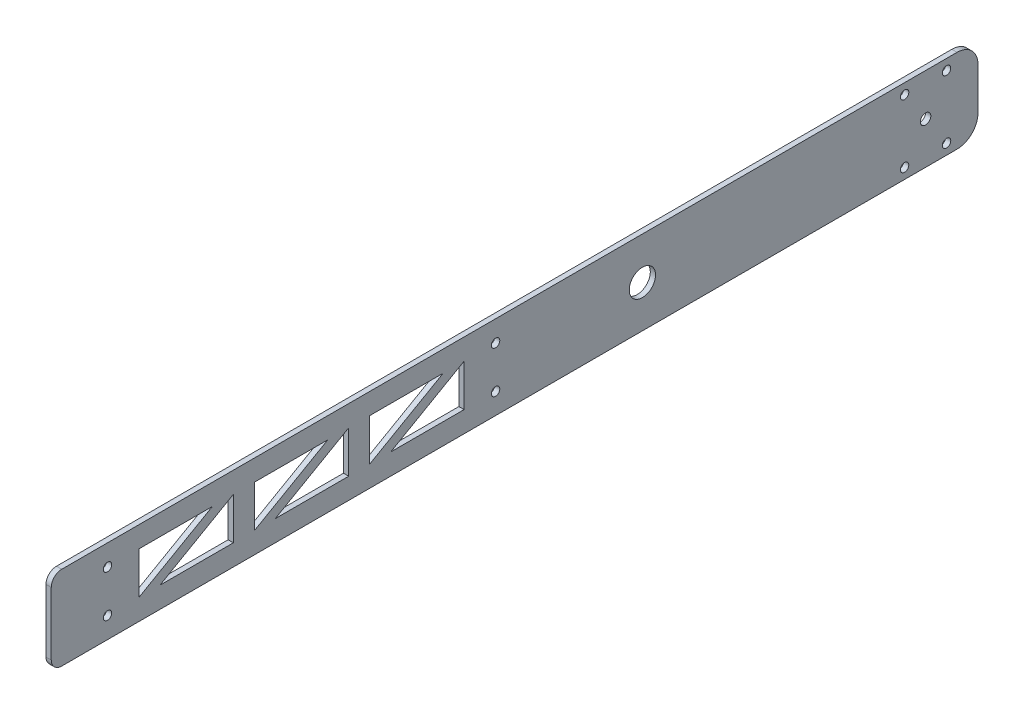
SolidWorks part; units mm, degrees
material "1060 Alloy"
ref_plane "Front Plane" through (0, 0, 0) normal (0, 0, 1) x (1, 0, 0)
ref_plane "Top Plane" through (0, 0, 0) normal (0, 1, 0) x (1, 0, 0)
ref_plane "Right Plane" through (0, 0, 0) normal (1, 0, 0) x (0, 0, -1)
sketch "Sketch1" plane through (0, 0, 0) normal (1, 0, 0) x (0, 0, -1)
  line L0 (177.8, 38.1) -> (177.8, 12.7)
  line L1 (165.1, 0) -> (-571.5, 0)
  line L2 (0, 0) -> (0, 50.8) construction
  line L3 (165.1, 50.8) -> (-571.5, 50.8)
  line L4 (-507.6587, 38.1) -> (372.0993, 38.1) construction
  line L5 (-584.2, 38.1) -> (-584.2, 12.7)
  line L6 (-663.1888, 12.7) -> (-221.2336, 12.7) construction
  line L7 (-190.5, 38.1) -> (-146.05, 38.1)
  line L8 (133.35, 44.45) -> (133.35, 6.35) construction
  line L9 (133.35, 6.35) -> (158.75, 6.35) construction
  line L10 (158.75, 6.35) -> (158.75, 44.45) construction
  line L11 (158.75, 44.45) -> (133.35, 44.45) construction
  line L25 (-349.25, 119.599) -> (-349.25, -64.072) construction
  line L26 (-133.35, 38.1) -> (-133.35, 12.7)
  line L27 (-133.35, 12.7) -> (-177.8, 12.7)
  line L28 (-177.8, 12.7) -> (-133.35, 38.1)
  line L30 (-146.05, 38.1) -> (-190.5, 12.7)
  line L31 (-190.5, 12.7) -> (-190.5, 38.1)
  line L32 (-203.2, 12.7) -> (-203.2, 38.1)
  line L33 (-247.65, 12.7) -> (-203.2, 12.7)
  line L34 (-203.2, 38.1) -> (-247.65, 12.7)
  line L35 (-215.9, 38.1) -> (-260.35, 12.7)
  line L36 (-260.35, 38.1) -> (-215.9, 38.1)
  line L37 (-260.35, 12.7) -> (-260.35, 38.1)
  line L38 (-273.05, 38.1) -> (-273.05, 12.7)
  line L39 (-317.5, 12.7) -> (-273.05, 38.1)
  line L40 (-273.05, 12.7) -> (-317.5, 12.7)
  line L41 (-330.2, 12.7) -> (-330.2, 38.1)
  line L42 (-330.2, 38.1) -> (-285.75, 38.1)
  line L43 (-285.75, 38.1) -> (-330.2, 12.7)
  circle A0 centre (-25.4, 25.4) radius 7.9629
  arc A1 (177.8, 12.7) -> (165.1, 0) centre (165.1, 12.7) cw
  arc A2 (165.1, 50.8) -> (177.8, 38.1) centre (165.1, 38.1) cw
  circle A3 centre (146.05, 25.4) radius 3.175
  circle A4 centre (-349.25, 38.1) radius 2.5527
  circle A5 centre (-349.25, 12.7) radius 2.5527
  circle A6 centre (-114.3, 38.1) radius 2.5527
  circle A7 centre (-114.3, 12.7) radius 2.5527
  circle A8 centre (133.35, 44.45) radius 2.5527
  circle A9 centre (158.75, 44.45) radius 2.5527
  circle A10 centre (158.75, 6.35) radius 2.5527
  arc A11 (-584.2, 12.7) -> (-571.5, 0) centre (-571.5, 12.7) ccw
  arc A12 (-584.2, 38.1) -> (-571.5, 50.8) centre (-571.5, 38.1) cw
  circle A13 centre (133.35, 6.35) radius 2.5527
  point P8 (177.8, 0)
  point P13 (-25.4, 25.4)
  point P14 (177.8, 50.8)
  dimension "D7" = 50.8
  dimension "D8" = 12.7
  dimension "D9" = 12.7
  dimension "D10" = 6.35
  dimension "D11" = 31.75
  dimension "D22" = 5.1054
  dimension "D25" = 12.7
  dimension "D26" = 234.95
  dimension "D23" = 5.1054
  dimension "D24" = 12.7
  dimension "D27" = 19.05
  dimension "D28" = 19.05
  dimension "D33" = 44.45
  dimension "D34" = 44.45
  dimension "D35" = 44.45
  dimension "D36" = 44.45
  dimension "D37" = 44.45
  dimension "D38" = 19.05
  dimension "D39" = 12.7
  dimension "D46" = 12.7
  dimension "D47" = 19.05
  dimension "D48" = 5.1054
  dimension "D13" = 19.05
  dimension "D15" = 12.7
  dimension "D16" = 12.7
  dimension "D17" = 12.7
  dimension "D19" = 15.9258
  dimension "D5" = 762
  dimension "D12" = 25.4
  dimension "D20" = 88.9
  dimension "D21" = 88.9
  dimension "D14" = 44.45
  dimension "D42" = 5.1054
  dimension "D43" = 5.1054
  dimension "D49" = 5.1054
  dimension "D50" = 5.1054
  dimension "D51" = 5.1054
  dimension "D2" = 25.4
  dimension "D3" = 177.8
  dimension "D4" = 25.4
  dimension "D6" = 0
  dimension "D18" = 12.7
  dimension "D29" = 12.7
  dimension "D30" = 12.7
  dimension "D31" = 12.7
  dimension "D32" = 25.4
  dimension "D40" = 12.7
  dimension "D41" = 12.7
  dimension "D44" = 25.4
  dimension "D45" = 38.1
extrude "Boss-Extrude1" add sketch "Sketch1" along normal blind 3.175
sketch "Sketch2" plane through (3.175, 0, 0) normal (1, 0, 0) x (0, 0, -1)
  line L0 (-558.8, 50.8) -> (-558.8, 0) construction
  line L1 (165.1, 50.8) -> (-571.5, 50.8) construction
  line L2 (-571.5, 0) -> (165.1, 0) construction
  line L3 (-584.2, 38.1) -> (-584.2, 12.7) construction
  circle A0 centre (-558.8, 25.4) radius 5.5563
  dimension "D2" = 11.1125
  dimension "D1" = 25.4
extrude "Cut-Extrude1" cut sketch "Sketch2" against normal through all
sketch "Sketch3" plane through (3.175, 0, 0) normal (1, 0, 0) x (0, 0, -1)
  line L0 (165.1, 50.8) -> (-571.5, 50.8) construction
  line L1 (-383.32, 50.8) -> (-584.2, 50.8)
  line L2 (-383.32, 50.8) -> (-383.32, 0)
  line L3 (-383.32, 0) -> (-584.2, 0)
  line L4 (-584.2, 50.8) -> (-584.2, 0)
  circle A0 centre (-349.25, 38.1) radius 2.5527 construction
  dimension "D1" = 34.07
  dimension "D2" = 200.88
  dimension "D3" = 50.8
extrude "Cut-Extrude2" cut sketch "Sketch3" against normal through all
fillet "Fillet1" radius 6.35 2 edges at (1.5875, 0, 383.32) (1.5875, 50.8, 383.32)
